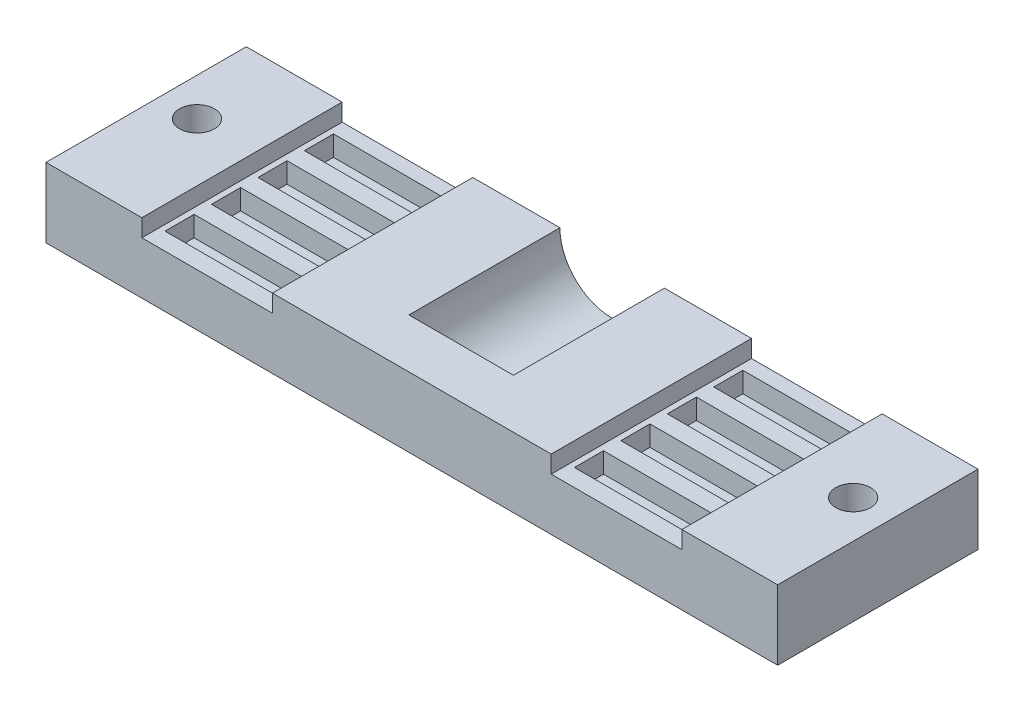
SolidWorks part; units mm, degrees
ref_plane "Alzado" through (0, 0, 0) normal (0, 0, 1) x (1, 0, 0)
ref_plane "Planta" through (0, 0, 0) normal (0, 1, 0) x (1, 0, 0)
ref_plane "Vista lateral" through (0, 0, 0) normal (1, 0, 0) x (0, 0, -1)
sketch "Croquis1" plane through (0, 0, 0) normal (0, 0, 1) x (1, 0, 0)
  line L0 (0, 0) -> (0, 12)
  line L1 (0, 12) -> (16.5, 12)
  line L2 (16.5, 12) -> (16.5, 9)
  line L3 (16.5, 9) -> (39, 9)
  line L4 (39, 9) -> (39, 12)
  line L5 (39, 12) -> (87, 12)
  line L6 (87, 12) -> (87, 9)
  line L7 (87, 9) -> (109.5, 9)
  line L8 (109.5, 9) -> (109.5, 12)
  line L9 (109.5, 12) -> (126, 12)
  line L10 (126, 12) -> (126, 0)
  line L11 (126, 0) -> (0, 0)
  dimension "D1" = 12
  dimension "D2" = 3
  dimension "D3" = 22.5
  dimension "D4" = 22.5
  dimension "D5" = 16.5
  dimension "D6" = 16.5
  dimension "D7" = 126
  dimension "D8" = 48
extrude "Saliente-Extruir1" add sketch "Croquis1" along normal blind 34.5
sketch "Croquis2" plane through (0, 0, 0) normal (0, 0, -1) x (-1, 0, 0)
  line L0 (-87, 12) -> (-39, 12) construction
  circle A0 centre (-63, 12) radius 9
extrude "Cortar-Extruir1" cut sketch "Croquis2" against normal blind 26
sketch "Croquis3" plane through (0, 9, 0) normal (0, 1, 0) x (1, 0, 0)
  line L0 (17.5, -31.5) -> (38, -31.5)
  line L1 (38, -31.5) -> (38, -26.5)
  line L2 (38, -26.5) -> (17.5, -26.5)
  line L3 (17.5, -26.5) -> (17.5, -31.5)
  line L4 (39, -34.5) -> (16.5, -34.5) construction
  line L5 (16.5, -34.5) -> (16.5, 0) construction
  line L7 (27.5, -31.5) -> (38, -31.5)
  line L9 (38, -26.5) -> (27.5, -26.5)
  line L11 (27.5, -23.5) -> (38, -23.5)
  line L13 (38, -18.5) -> (27.5, -18.5)
  line L15 (27.5, -15.5) -> (38, -15.5)
  line L17 (38, -10.5) -> (27.5, -10.5)
  line L19 (27.5, -7.5) -> (38, -7.5)
  line L21 (38, -2.5) -> (27.5, -2.5)
  line L22 (17.5, -18.5) -> (17.5, -23.5)
  line L23 (17.5, -23.5) -> (38, -23.5)
  line L24 (38, -23.5) -> (38, -18.5)
  line L25 (38, -18.5) -> (17.5, -18.5)
  line L26 (17.5, -10.5) -> (17.5, -15.5)
  line L27 (17.5, -15.5) -> (38, -15.5)
  line L28 (38, -15.5) -> (38, -10.5)
  line L29 (38, -10.5) -> (17.5, -10.5)
  line L30 (17.5, -2.5) -> (17.5, -7.5)
  line L31 (17.5, -7.5) -> (38, -7.5)
  line L32 (38, -7.5) -> (38, -2.5)
  line L33 (38, -2.5) -> (17.5, -2.5)
  line L34 (48, -7.5) -> (48, -2.5) [skipped]
  line L35 (48, -15.5) -> (48, -10.5) [skipped]
  line L36 (48, -23.5) -> (48, -18.5) [skipped]
  line L37 (48, -31.5) -> (48, -26.5) [skipped]
  line L38 (27.5, -26.5) -> (27.5, -31.5) [skipped]
  line L39 (27.5, -18.5) -> (27.5, -23.5) [skipped]
  line L40 (27.5, -10.5) -> (27.5, -15.5) [skipped]
  line L41 (27.5, -2.5) -> (27.5, -7.5) [skipped]
  line L43 (63, -34.5) -> (63, 2.3788) construction
  line L44 (87, -34.5) -> (39, -34.5) construction
  line L45 (88, -26.5) -> (108.5, -26.5)
  line L46 (88, -31.5) -> (88, -26.5)
  line L47 (108.5, -31.5) -> (88, -31.5)
  line L48 (108.5, -26.5) -> (108.5, -31.5)
  line L49 (88, -18.5) -> (108.5, -18.5)
  line L50 (88, -23.5) -> (88, -18.5)
  line L51 (108.5, -23.5) -> (88, -23.5)
  line L52 (108.5, -18.5) -> (108.5, -23.5)
  line L53 (88, -10.5) -> (108.5, -10.5)
  line L54 (88, -15.5) -> (88, -10.5)
  line L55 (108.5, -15.5) -> (88, -15.5)
  line L56 (108.5, -10.5) -> (108.5, -15.5)
  line L57 (88, -2.5) -> (108.5, -2.5)
  line L58 (88, -7.5) -> (88, -2.5)
  line L59 (108.5, -7.5) -> (88, -7.5)
  line L60 (108.5, -2.5) -> (108.5, -7.5)
  dimension "D1" = 20.5
  dimension "D2" = 5
  dimension "D3" = 3
  dimension "D4" = 1
  dimension "D5" = 4
  dimension "D6" = 2
extrude "Cortar-Extruir2" cut sketch "Croquis3" against normal blind 3.5 contours L2 L3 L0 L1 | L13 L25 L22 L23 L11 L24 | L17 L29 L26 L27 L15 L28 | L21 L33 L30 L31 L19 L32 | L48 L45 L46 L47 | L52 L49 L50 L51 | L56 L53 L54 L55 | L60 L57 L58 L59
sketch "Croquis4" plane through (0, 12, 0) normal (0, 1, 0) x (1, 0, 0)
  line L0 (6.5, -15) -> (0, -15) construction
  line L2 (6.5, -15) -> (6.5, 0) construction
  line L5 (16.5, 0) -> (0, 0) construction
  line L6 (0, -34.5) -> (0, 0) construction
  circle A0 centre (6.5, -15) radius 3
  dimension "D1" = 15
extrude "Cortar-Extruir3" cut sketch "Croquis4" against normal through all
ref_plane "Plano1" through (63, 0, 0) normal (-1, 0, 0) x (0, 0, 1)
mirror "Simetría1" about plane through (63, 0, 0) normal (-1, 0, 0) of "Cortar-Extruir3"
